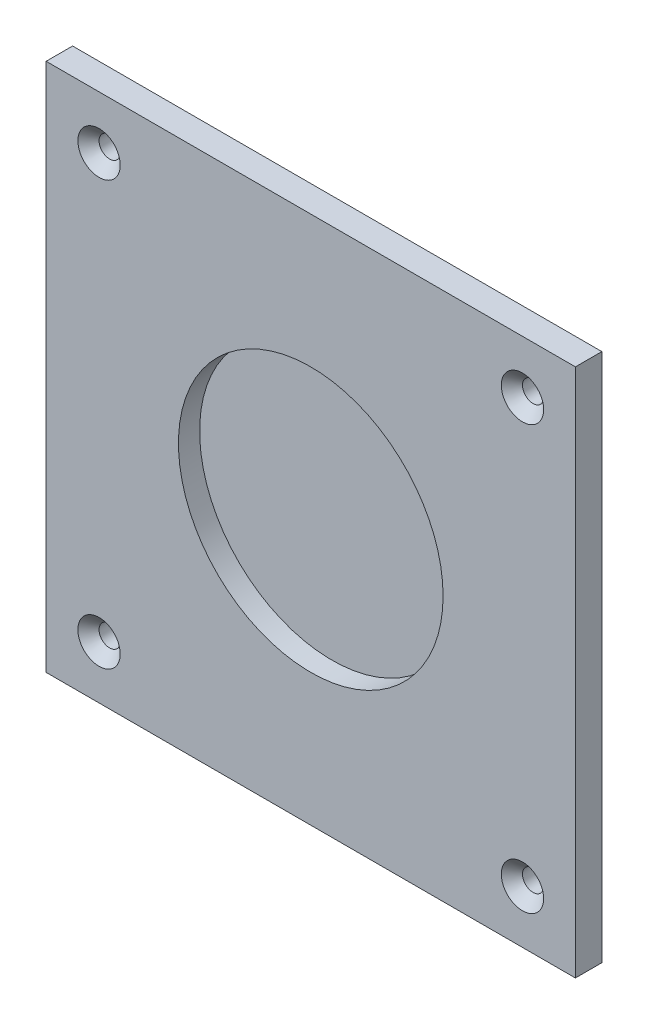
SolidWorks part; units mm, degrees
ref_plane "Front Plane" through (0, 0, 0) normal (0, 0, 1) x (1, 0, 0)
ref_plane "Top Plane" through (0, 0, 0) normal (0, 1, 0) x (1, 0, 0)
ref_plane "Right Plane" through (0, 0, 0) normal (1, 0, 0) x (0, 0, -1)
sketch "Sketch1" plane through (0, 0, 0) normal (0, 0, 1) x (1, 0, 0)
  line L1 (1270, -1270) -> (-1270, -1270)
  line L2 (1270, -1270) -> (1270, 1270)
  line L3 (1270, 1270) -> (-1270, 1270)
  line L4 (-1270, -1270) -> (-1270, 1270)
  line L5 (1270, -1270) -> (-1270, 1270) construction
  line L6 (1270, 1270) -> (-1270, -1270) construction
  point P1 (0, 0)
  dimension "D1" = 2540
  dimension "D2" = 2540
extrude "Boss-Extrude1" add sketch "Sketch1" against normal blind 127
sketch "Sketch2" plane through (0, 0, 0) normal (0, 0, 1) x (1, 0, 0)
  circle A0 centre (0, 0) radius 635
  dimension "D1" = 1270
extrude "Cut-Extrude1" cut sketch "Sketch2" against normal blind 101.6
ref_plane "Plane1" through (1016, 0, 0) normal (1, 0, 0) x (0, 0, -1)
sketch "Sketch3" plane through (1016, 0, 0) normal (1, 0, 0) x (0, 0, -1)
  line L0 (127, 1066.8) -> (50.8, 1066.8)
  line L1 (127, -1270) -> (127, 1270) construction
  line L2 (50.8, 1066.8) -> (0, 1117.6)
  line L3 (0, -1270) -> (0, 1270) construction
  line L4 (127, 1016) -> (0, 1016)
  line L5 (127, 1066.8) -> (127, 1016)
  line L6 (0, 1117.6) -> (0, 1016)
  dimension "D1" = 50.8
  dimension "D2" = 101.6
  dimension "D3" = 45
  dimension "D4" = 1016
revolve "Cut-Revolve1" cut sketch "Sketch3" angle 360 about L4
pattern_circular "CirPattern1" count 4 over 360 about axis through (0, 0, 0) along (0, 0, 1) of "Cut-Revolve1"
